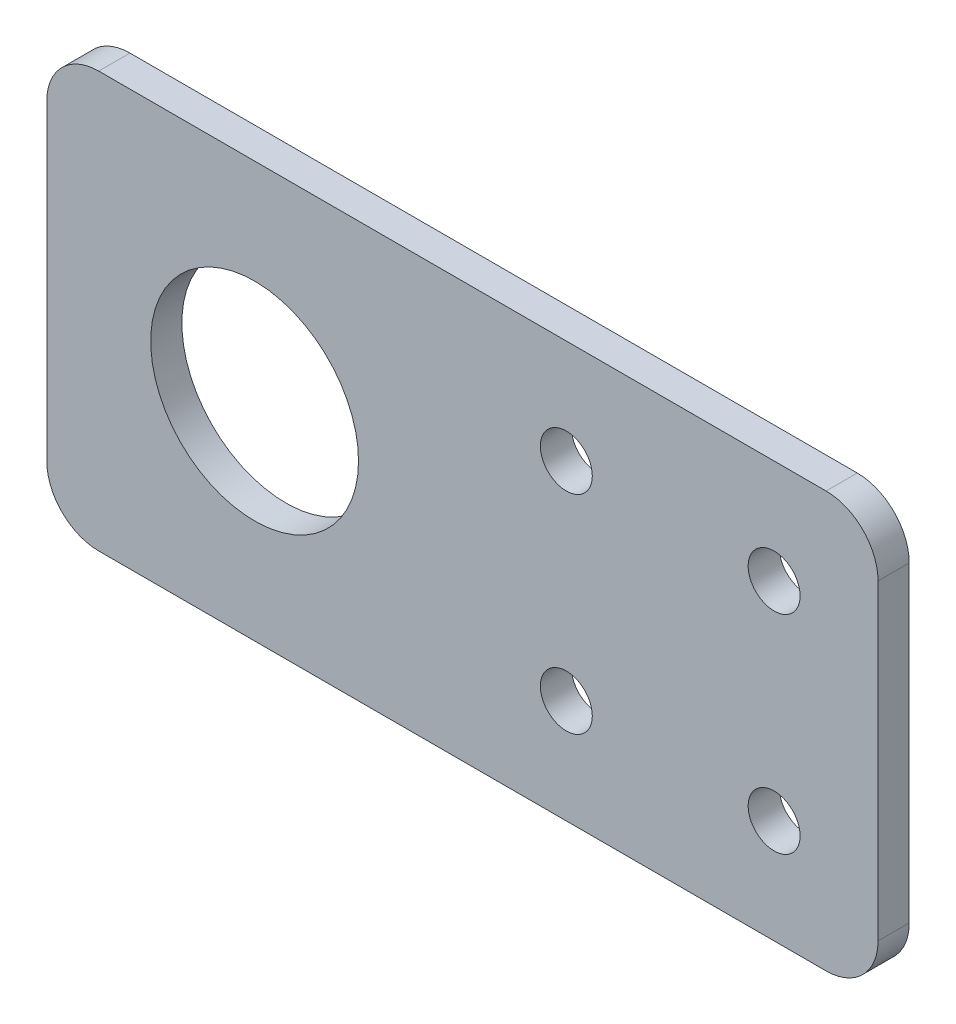
SolidWorks part; units mm, degrees
ref_plane "Front Plane" through (0, 0, 0) normal (0, 0, 1) x (1, 0, 0)
ref_plane "Top Plane" through (0, 0, 0) normal (0, 1, 0) x (1, 0, 0)
ref_plane "Right Plane" through (0, 0, 0) normal (1, 0, 0) x (0, 0, -1)
sketch "Sketch1" plane through (0, 0, 0) normal (0, 0, 1) x (1, 0, 0)
  line L1 (-80, 20) -> (0, 20)
  line L2 (-80, 20) -> (-80, -20)
  line L3 (-80, -20) -> (0, -20)
  line L4 (0, 20) -> (0, -20)
  circle A0 centre (-60, 0) radius 10
  circle A1 centre (-10, 10) radius 2.5
  circle A2 centre (-10, -10) radius 2.5
  circle A3 centre (-30, -10) radius 2.5
  circle A4 centre (-30, 10) radius 2.5
  point P4 (0, 0)
  dimension "D3" = 5
  dimension "D4" = 20
  dimension "D5" = 10
  dimension "D6" = 20
  dimension "D7" = 10
  dimension "D8" = 20
  dimension "D9" = 20
  dimension "D1" = 40
  dimension "D2" = 80
extrude "Boss-Extrude1" add sketch "Sketch1" along normal blind 3
fillet "Fillet1" radius 5 4 edges at (0, -20, 1.5) (0, 20, 1.5) (-80, -20, 1.5) (-80, 20, 1.5)
